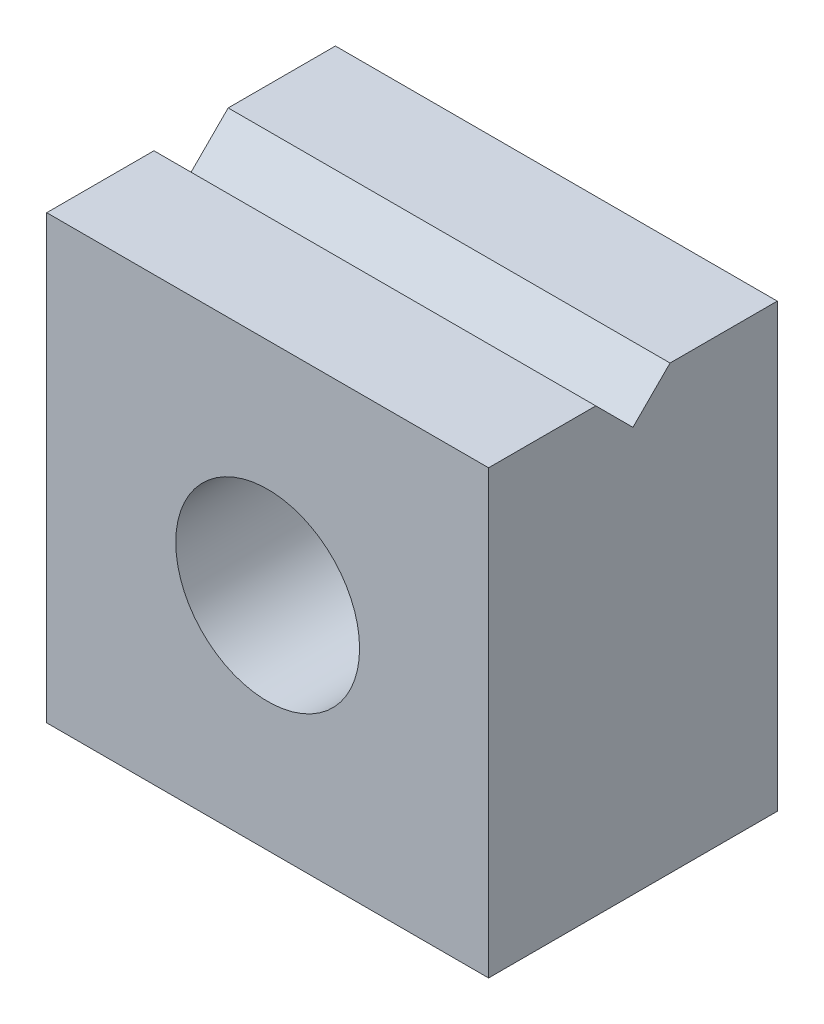
SolidWorks part; units mm, degrees
material "1023 Carbon Steel Sheet (SS)"
ref_plane "Front Plane" through (0, 0, 0) normal (0, 0, 1) x (1, 0, 0)
ref_plane "Top Plane" through (0, 0, 0) normal (0, 1, 0) x (1, 0, 0)
ref_plane "Right Plane" through (0, 0, 0) normal (1, 0, 0) x (0, 0, -1)
sketch "Sketch1" plane through (0, 0, 0) normal (0, 0, 1) x (1, 0, 0)
  line L1 (-3.75, -3.75) -> (3.75, -3.75)
  line L2 (-3.75, -3.75) -> (-3.75, 3.75)
  line L3 (-3.75, 3.75) -> (3.75, 3.75)
  line L4 (3.75, -3.75) -> (3.75, 3.75)
  line L5 (-3.75, -3.75) -> (3.75, 3.75) construction
  line L6 (-3.75, 3.75) -> (3.75, -3.75) construction
  circle A0 centre (0, 0) radius 1.56
  point P0 (0, 0)
  dimension "D2" = 3.12
  dimension "D1" = 7.5
extrude "Boss-Extrude1" add sketch "Sketch1" along normal blind 4.9
sketch "Sketch5" plane through (0, 0, 0) normal (1, 0, 0) x (0, 0, -1)
  line L0 (0, 0) -> (-4.9, 0) construction
  line L1 (-4.9, -3.75) -> (-4.9, 3.75) construction
  line L2 (-2.45, 0) -> (-2.45, 3.75) construction
  line L3 (-4.9, 3.75) -> (0, 3.75) construction
  line L4 (-2.45, 3.12) -> (-3.08, 3.75)
  line L5 (-3.08, 3.75) -> (-1.82, 3.75)
  line L6 (-2.45, 3.12) -> (-1.82, 3.75)
  dimension "D1" = 90
  dimension "D2" = 0.63
extrude "Cut-Extrude1" cut sketch "Sketch5" against normal through all both and the other way through all
